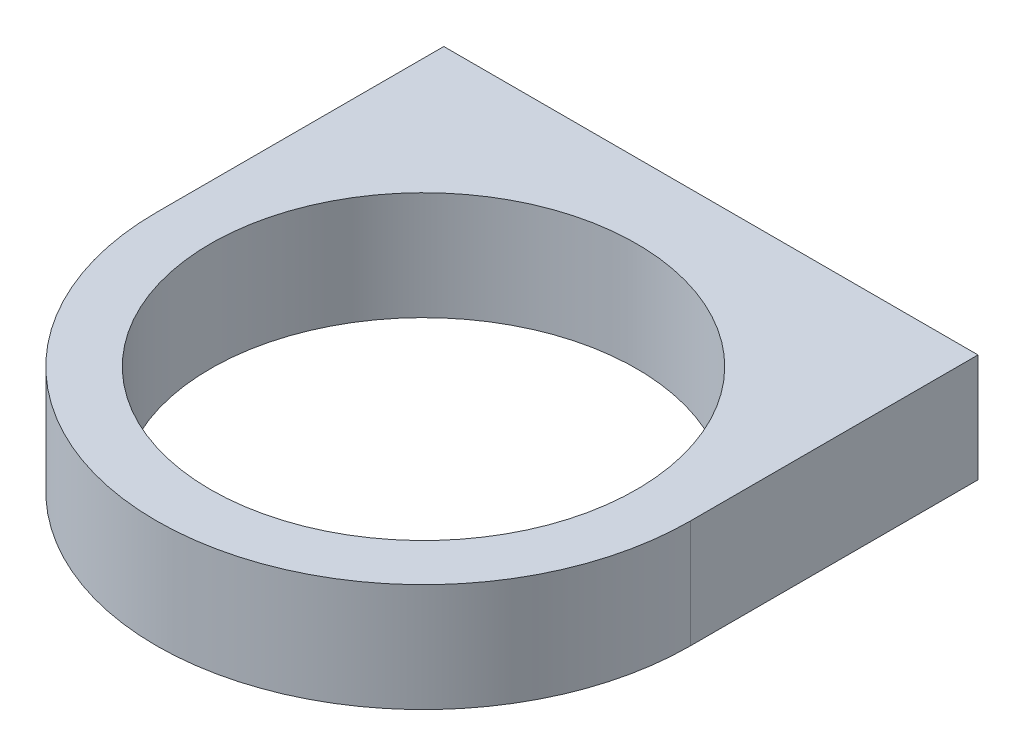
SolidWorks part; units mm, degrees
ref_plane "Front Plane" through (0, 0, 0) normal (0, 0, 1) x (1, 0, 0)
ref_plane "Top Plane" through (0, 0, 0) normal (0, 1, 0) x (1, 0, 0)
ref_plane "Right Plane" through (0, 0, 0) normal (1, 0, 0) x (0, 0, -1)
sketch "Sketch18" plane through (0, 0, 0) normal (0, 1, 0) x (1, 0, 0)
  line L0 (-39.5, 0) -> (-39.5, 42.5)
  line L1 (-39.5, 42.5) -> (39.5, 42.5)
  line L2 (39.5, 42.5) -> (39.5, 0)
  circle A0 centre (0, 0) radius 31.5
  arc A1 (-39.5, 0) -> (39.5, 0) centre (0, 0) ccw
  dimension "D1" = 63
  dimension "D2" = 8
  dimension "D3" = 42.5
extrude "Boss-Extrude13" add sketch "Sketch18" along normal blind 16
sketch "Sketch19" plane through (0, 0, 0) normal (0, -1, 0) x (1, 0, 0)
  line L0 (39.5, -42.5) -> (-39.5, -42.5) construction
  line L1 (-39.5, -42.5) -> (-39.5, 0) construction
  line L2 (39.5, 0) -> (39.5, -42.5) construction
  circle A0 centre (-35.5, -38.5) radius 2
  circle A1 centre (35.5, -38.5) radius 2
  dimension "D1" = 4
  dimension "D2" = 4
  dimension "D3" = 4
  dimension "D4" = 4
extrude "Boss-Extrude14" add sketch "Sketch19" along normal blind 2
